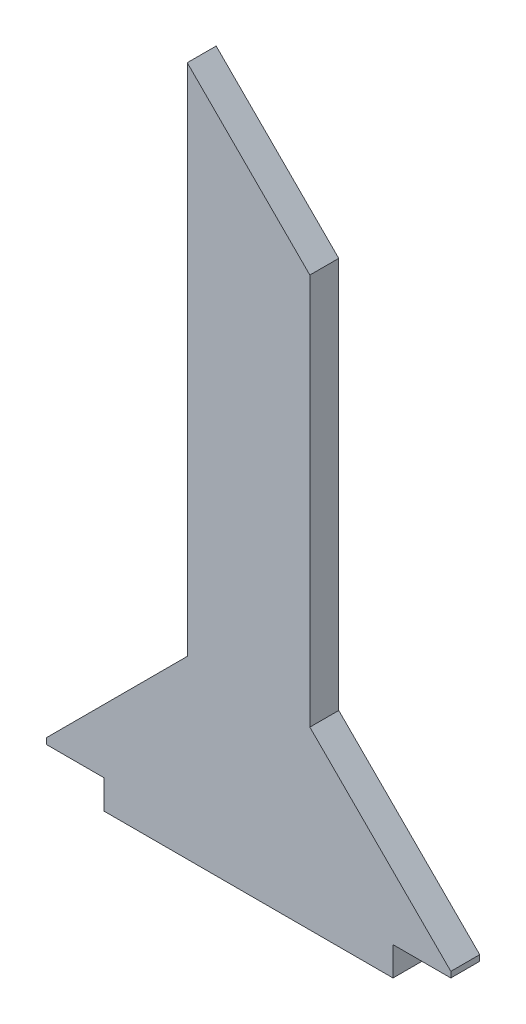
SolidWorks part; units mm, degrees
ref_plane "Front Plane" through (0, 0, 0) normal (0, 0, 1) x (1, 0, 0)
ref_plane "Top Plane" through (0, 0, 0) normal (0, 1, 0) x (1, 0, 0)
ref_plane "Right Plane" through (0, 0, 0) normal (1, 0, 0) x (0, 0, -1)
sketch "Sketch1" plane through (0, 0, 0) normal (0, 0, 1) x (1, 0, 0)
  line L0 (150, -163.7868) -> (350, -163.7868)
  line L1 (350, -163.7868) -> (350, -143.7868)
  line L2 (150, -163.7868) -> (150, -143.7868)
  line L3 (150, -143.7868) -> (110, -143.7868)
  line L4 (250, -163.7868) -> (250, 720.769) construction
  line L5 (0, 0) -> (500, 0) construction
  line L6 (500, 0) -> (6.974, 493.026) construction
  line L7 (500, 0) -> (743.5146, 0) construction
  line L8 (521.2132, 0) -> (-23.259, 544.4722) construction
  line L9 (521.2132, 0) -> (535.3553, 14.1421) construction
  line L10 (0, 0) -> (0, 744.8677) construction
  line L11 (535.3553, 14.1421) -> (-9.1169, 558.6144) construction
  line L12 (-9.1169, 558.6144) -> (-23.259, 544.4722) construction
  line L13 (-2.0458, 523.259) -> (2.1968, 527.5017) construction
  line L14 (2.1968, 527.5017) -> (504.2426, 25.4558) construction
  line L15 (504.2426, 25.4558) -> (500, 21.2132) construction
  line L16 (350, -143.7868) -> (390, -143.7868)
  line L17 (390, -143.7868) -> (390, -139.7868)
  line L18 (390, -139.7868) -> (292.4264, -42.2132)
  line L19 (292.4264, -42.2132) -> (292.4264, 228.7868)
  line L20 (110, -143.7868) -> (110, -139.7868)
  line L21 (110, -139.7868) -> (207.5736, -42.2132)
  line L22 (207.5736, -42.2132) -> (207.5736, 313.6396)
  line L23 (207.5736, 313.6396) -> (292.4264, 228.7868)
  line L24 (250, 271.2132) -> (250, 346.932) construction
  line L25 (0, 0) -> (-702.8302, 0) construction
  line L26 (-704.4199, 656.2132) -> (-704.4199, -113.7868) construction
  line L27 (-23.259, 544.4722) -> (-706.1669, 544.4722) construction
  line L28 (-782.2872, -143.7868) -> (743.5146, -143.7868) construction
  line L29 (250, 271.2132) -> (-704.4199, 271.2132) construction
  dimension "D1" = 200
  dimension "D2" = 20
  dimension "D3" = 500
  dimension "D4" = 250
  dimension "D5" = 45
  dimension "D6" = 770
  dimension "D7" = 6
  dimension "D8" = 20
  dimension "D9" = 710
  dimension "D10" = 30
  dimension "D11" = 4
  dimension "D12" = 4
  dimension "D13" = 40
  dimension "D14" = 40
  dimension "D15" = 120
  dimension "D16" = 770
  dimension "D17" = 544.4722
  dimension "D18" = 30
extrude "Boss-Extrude1" add sketch "Sketch1" along normal blind 20
